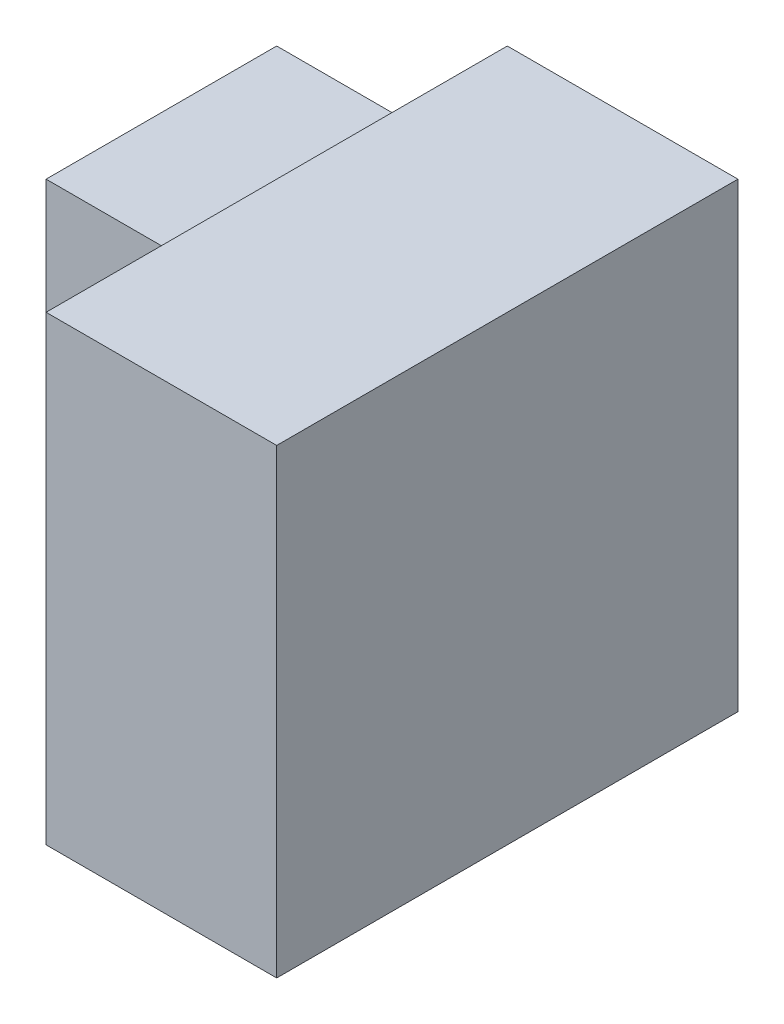
SolidWorks part; units mm, degrees
ref_plane "Front Plane" through (0, 0, 0) normal (0, 0, 1) x (1, 0, 0)
ref_plane "Top Plane" through (0, 0, 0) normal (0, 1, 0) x (1, 0, 0)
ref_plane "Right Plane" through (0, 0, 0) normal (1, 0, 0) x (0, 0, -1)
sketch "Sketch1" plane through (0, 0, 0) normal (1, 0, 0) x (0, 0, -1)
  line L1 (0, 0) -> (4, 0)
  line L2 (0, 0) -> (0, 4)
  line L3 (0, 4) -> (4, 4)
  line L4 (4, 0) -> (4, 4)
  dimension "D1" = 4
  dimension "D2" = 4
extrude "Boss-Extrude1" add sketch "Sketch1" along normal blind 2
sketch "Sketch2" plane through (0, 0, 0) normal (-1, 0, 0) x (0, 0, 1)
  line L1 (-4, 0) -> (-2, 0)
  line L2 (-4, 0) -> (-4, 3)
  line L3 (-4, 3) -> (-2, 3)
  line L4 (-2, 0) -> (-2, 3)
  dimension "D1" = 3
  dimension "D2" = 2
extrude "Boss-Extrude2" add sketch "Sketch2" along normal blind 2
